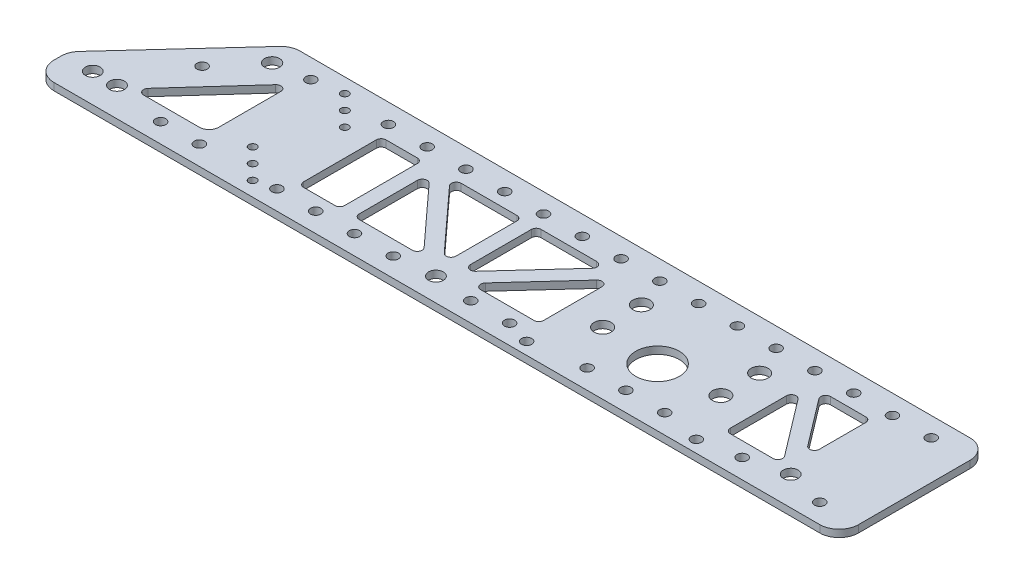
SolidWorks part; units mm, degrees
ref_plane "Front Plane" through (0, 0, 0) normal (0, 0, 1) x (1, 0, 0)
ref_plane "Top Plane" through (0, 0, 0) normal (0, 1, 0) x (1, 0, 0)
ref_plane "Right Plane" through (0, 0, 0) normal (1, 0, 0) x (0, 0, -1)
ref_plane "Plane1" through (0, 0, 0) normal (0, -1, 0) x (1, 0, 0)
sketch "Sketch1" plane through (0, 0, 0) normal (0, -1, 0) x (1, 0, 0)
  line L0 (3.3381, -25.8666) -> (66.0749, -94.3067)
  line L1 (75.4368, -98.425) -> (514.35, -98.425)
  line L2 (527.05, -85.725) -> (527.05, -12.7)
  line L3 (514.35, 0) -> (12.7, 0)
  line L4 (0, -12.7) -> (0, -17.2849)
  line L5 (49.2335, -22.225) -> (85.725, -22.225)
  line L6 (92.075, -28.575) -> (92.075, -69.2419)
  line L7 (86.5456, -71.372) -> (46.8792, -27.5301)
  line L8 (174.531, -76.2) -> (153.9875, -76.2)
  line L9 (150.8125, -73.025) -> (150.8125, -25.4)
  line L10 (153.9875, -22.225) -> (174.531, -22.225)
  line L11 (177.706, -25.4) -> (177.706, -73.025)
  line L12 (227.626, -27.5424) -> (192.7492, -65.687)
  line L13 (187.231, -63.5446) -> (187.231, -25.4)
  line L14 (190.406, -22.225) -> (225.2828, -22.225)
  line L15 (252.4125, -73.025) -> (252.4125, -33.1442)
  line L16 (257.9307, -31.0017) -> (294.3949, -70.8826)
  line L17 (292.0517, -76.2) -> (255.5875, -76.2)
  line L18 (239.7125, -76.2) -> (203.2483, -76.2)
  line L19 (200.9051, -70.8826) -> (237.3693, -31.0017)
  line L20 (242.8875, -33.1442) -> (242.8875, -73.025)
  line L21 (270.0172, -22.225) -> (304.894, -22.225)
  line L22 (308.069, -25.4) -> (308.069, -63.5446)
  line L23 (302.5508, -65.687) -> (267.674, -27.5424)
  line L24 (433.5069, -22.225) -> (461.453, -22.225)
  line L25 (463.9807, -27.3213) -> (436.0346, -64.087)
  line L26 (430.3319, -62.1657) -> (430.3319, -25.4)
  line L27 (442.6654, -71.1037) -> (465.7848, -40.688)
  line L28 (471.4875, -42.6093) -> (471.4875, -73.025)
  line L29 (468.3125, -76.2) -> (445.1931, -76.2)
  circle A0 centre (34.925, -19.05) radius 4.826
  circle A1 centre (476.25, -19.05) radius 4.826
  circle A2 centre (19.05, -19.05) radius 4.826
  circle A3 centre (247.65, -15.24) radius 4.826
  circle A4 centre (369.9942, -38.1) radius 14.2812
  circle A5 centre (314.419, -7.9248) radius 3.3528
  circle A6 centre (425.5694, -7.9248) radius 3.3528
  arc A7 (66.0749, -94.3067) -> (75.4368, -98.425) centre (75.4368, -85.725) ccw
  arc A8 (514.35, -98.425) -> (527.05, -85.725) centre (514.35, -85.725) ccw
  arc A9 (527.05, -12.7) -> (514.35, 0) centre (514.35, -12.7) ccw
  arc A10 (12.7, 0) -> (0, -12.7) centre (12.7, -12.7) ccw
  arc A11 (0, -17.2849) -> (3.3381, -25.8666) centre (12.7, -17.2849) ccw
  circle A12 centre (73.025, -82.55) radius 4.953
  circle A13 centre (95.25, -12.7) radius 3.3782
  circle A14 centre (95.25, -85.725) radius 3.3782
  circle A15 centre (146.05, -12.7) radius 3.3782
  circle A16 centre (146.05, -85.725) radius 3.3782
  circle A17 centre (171.45, -12.7) radius 3.3782
  circle A18 centre (171.45, -85.725) radius 3.3782
  circle A19 centre (196.85, -12.7) radius 3.3782
  circle A20 centre (196.85, -85.725) radius 3.3782
  circle A21 centre (222.25, -12.7) radius 3.3782
  circle A22 centre (222.25, -85.725) radius 3.3782
  circle A23 centre (247.65, -85.725) radius 3.3782
  circle A24 centre (273.05, -12.7) radius 3.3782
  circle A25 centre (273.05, -85.725) radius 3.3782
  circle A26 centre (298.45, -12.7) radius 3.3782
  circle A27 centre (298.45, -85.725) radius 3.3782
  circle A28 centre (323.85, -85.725) radius 3.3782
  circle A29 centre (349.25, -12.7) radius 3.3782
  circle A30 centre (349.25, -85.725) radius 3.3782
  circle A31 centre (374.65, -12.7) radius 3.3782
  circle A32 centre (374.65, -85.725) radius 3.3782
  circle A33 centre (400.05, -12.7) radius 3.3782
  circle A34 centre (400.05, -85.725) radius 3.3782
  circle A35 centre (425.45, -85.725) radius 3.3782
  circle A36 centre (450.85, -12.7) radius 3.3782
  circle A37 centre (450.85, -85.725) radius 3.3782
  circle A38 centre (476.25, -85.725) radius 3.3782
  circle A39 centre (501.65, -12.7) radius 3.3782
  circle A40 centre (501.65, -85.725) radius 3.3782
  circle A41 centre (123.825, -19.05) radius 2.5527
  circle A42 centre (114.3, -28.575) radius 2.5527
  circle A43 centre (133.35, -9.525) radius 2.5527
  circle A44 centre (114.3, -88.9) radius 2.5527
  circle A45 centre (123.825, -79.375) radius 2.5527
  circle A46 centre (133.35, -69.85) radius 2.5527
  circle A47 centre (331.2592, -40.8178) radius 5.5626
  circle A48 centre (408.7292, -66.2178) radius 5.5626
  circle A49 centre (331.2592, -66.2178) radius 5.5626
  circle A50 centre (408.7292, -40.8178) radius 5.5626
  arc A51 (46.8792, -27.5301) -> (49.2335, -22.225) centre (49.2335, -25.4) cw
  arc A52 (85.725, -22.225) -> (92.075, -28.575) centre (85.725, -28.575) cw
  arc A53 (92.075, -69.2419) -> (86.5456, -71.372) centre (88.9, -69.2419) cw
  arc A54 (177.706, -73.025) -> (174.531, -76.2) centre (174.531, -73.025) cw
  arc A55 (153.9875, -76.2) -> (150.8125, -73.025) centre (153.9875, -73.025) cw
  arc A56 (150.8125, -25.4) -> (153.9875, -22.225) centre (153.9875, -25.4) cw
  arc A57 (174.531, -22.225) -> (177.706, -25.4) centre (174.531, -25.4) cw
  arc A58 (225.2828, -22.225) -> (227.626, -27.5424) centre (225.2828, -25.4) cw
  arc A59 (192.7492, -65.687) -> (187.231, -63.5446) centre (190.406, -63.5446) cw
  arc A60 (187.231, -25.4) -> (190.406, -22.225) centre (190.406, -25.4) cw
  arc A61 (255.5875, -76.2) -> (252.4125, -73.025) centre (255.5875, -73.025) cw
  arc A62 (252.4125, -33.1442) -> (257.9307, -31.0017) centre (255.5875, -33.1442) cw
  arc A63 (294.3949, -70.8826) -> (292.0517, -76.2) centre (292.0517, -73.025) cw
  arc A64 (242.8875, -73.025) -> (239.7125, -76.2) centre (239.7125, -73.025) cw
  arc A65 (203.2483, -76.2) -> (200.9051, -70.8826) centre (203.2483, -73.025) cw
  arc A66 (237.3693, -31.0017) -> (242.8875, -33.1442) centre (239.7125, -33.1442) cw
  arc A67 (267.674, -27.5424) -> (270.0172, -22.225) centre (270.0172, -25.4) cw
  arc A68 (304.894, -22.225) -> (308.069, -25.4) centre (304.894, -25.4) cw
  arc A69 (308.069, -63.5446) -> (302.5508, -65.687) centre (304.894, -63.5446) cw
  arc A70 (430.3319, -25.4) -> (433.5069, -22.225) centre (433.5069, -25.4) cw
  arc A71 (461.453, -22.225) -> (463.9807, -27.3213) centre (461.453, -25.4) cw
  arc A72 (436.0346, -64.087) -> (430.3319, -62.1657) centre (433.5069, -62.1657) cw
  arc A73 (445.1931, -76.2) -> (442.6654, -71.1037) centre (445.1931, -73.025) cw
  arc A74 (465.7848, -40.688) -> (471.4875, -42.6093) centre (468.3125, -42.6093) cw
  arc A75 (471.4875, -73.025) -> (468.3125, -76.2) centre (468.3125, -73.025) cw
  circle A76 centre (69.85, -12.7) radius 3.3782
  circle A77 centre (51.9505, -57.7565) radius 3.3782
extrude "Boss-Extrude1" add sketch "Sketch1" against normal blind 4.7625
